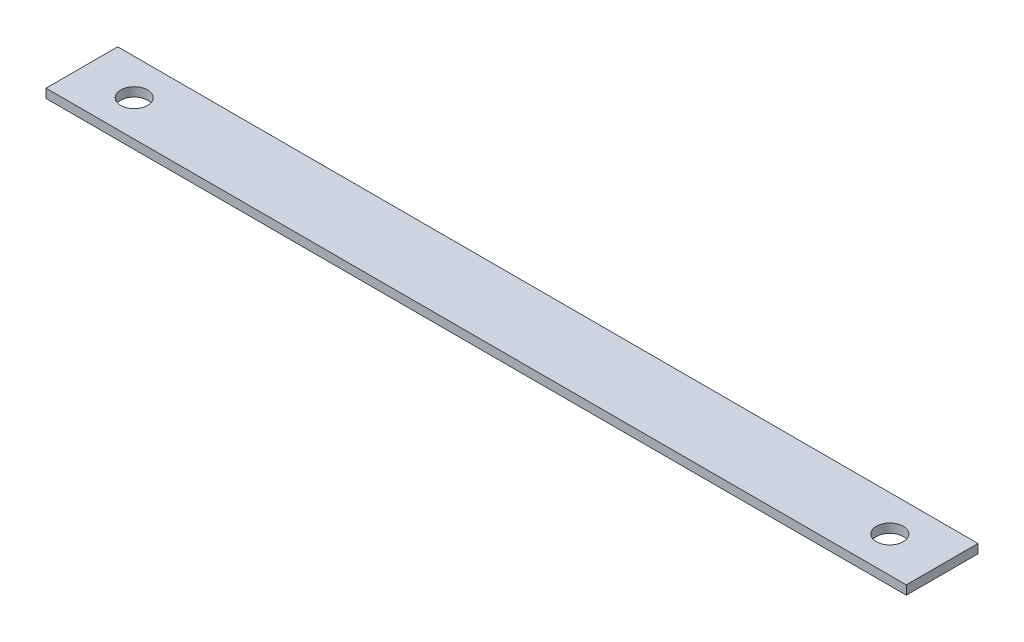
SolidWorks part; units mm, degrees
ref_plane "Front Plane" through (0, 0, 0) normal (0, 0, 1) x (1, 0, 0)
ref_plane "Top Plane" through (0, 0, 0) normal (0, 1, 0) x (1, 0, 0)
ref_plane "Right Plane" through (0, 0, 0) normal (1, 0, 0) x (0, 0, -1)
sketch "Sketch1" plane through (0, 0, 0) normal (0, 1, 0) x (1, 0, 0)
  line L1 (-152.4, 12.7) -> (152.4, 12.7)
  line L2 (-152.4, 12.7) -> (-152.4, -12.7)
  line L3 (-152.4, -12.7) -> (152.4, -12.7)
  line L4 (152.4, 12.7) -> (152.4, -12.7)
  line L5 (-152.4, 12.7) -> (152.4, -12.7) construction
  line L6 (-152.4, -12.7) -> (152.4, 12.7) construction
  point P0 (0, 0)
  dimension "D1" = 304.8
  dimension "D2" = 25.4
extrude "Boss-Extrude1" add sketch "Sketch1" along normal blind 3.175
sketch "Sketch2" plane through (0, 3.175, 0) normal (0, 1, 0) x (1, 0, 0)
  line L0 (0, 0) -> (-133.858, 0) construction
  line L1 (0, 0) -> (0, -12.7) construction
  line L2 (-152.4, -12.7) -> (152.4, -12.7) construction
  circle A0 centre (-133.858, 0) radius 4.7625
  circle A1 centre (133.858, 0) radius 4.7625
  dimension "D1" = 9.525
  dimension "D2" = 133.858
extrude "Cut-Extrude1" cut sketch "Sketch2" against normal through all
